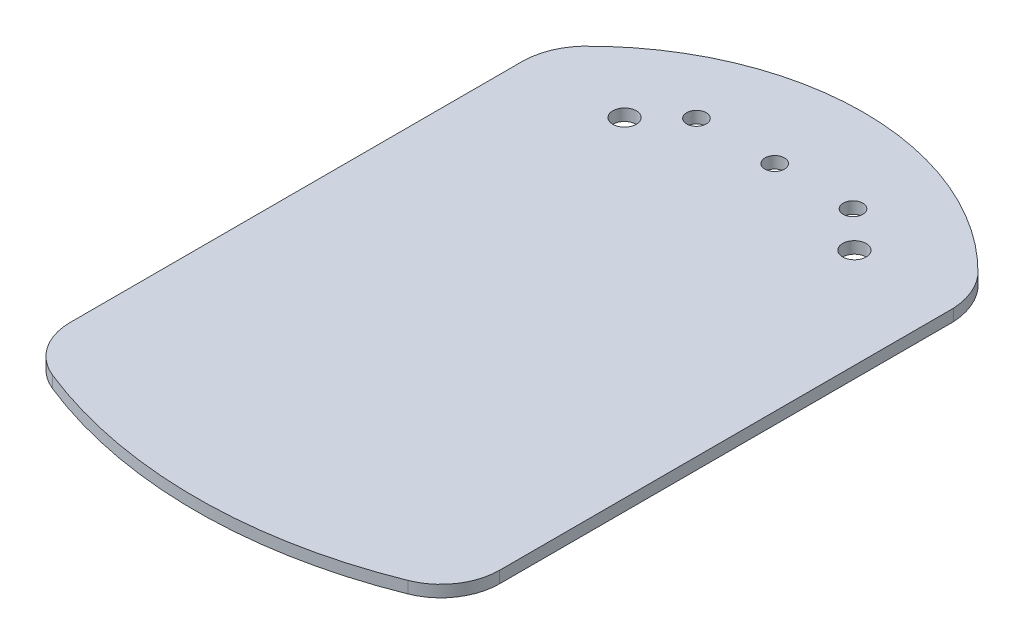
SolidWorks part; units mm, degrees
ref_plane "Front Plane" through (0, 0, 0) normal (0, 0, 1) x (1, 0, 0)
ref_plane "Top Plane" through (0, 0, 0) normal (0, 1, 0) x (1, 0, 0)
ref_plane "Right Plane" through (0, 0, 0) normal (1, 0, 0) x (0, 0, -1)
sketch "Sketch2" plane through (0, 0, 0) normal (0, 1, 0) x (1, 0, 0)
  line L0 (0, 42.2024) -> (20, 42.2024) construction
  line L2 (-54.8439, -82.9506) -> (-54.8439, 33.0807)
  line L4 (54.8439, -82.9506) -> (54.8439, 33.0807)
  line L5 (-38.4122, -53.1213) -> (35.0784, 48.5109) construction
  line L6 (-35.0784, 48.5109) -> (38.4122, -53.1213) construction
  line L7 (0, 42.2024) -> (-20, 42.2024) construction
  arc A0 (-50.5821, 43.5541) -> (50.5821, 43.5541) centre (0, -5.7807) cw
  arc A1 (-45.432, -96.8708) -> (45.432, -96.8708) centre (0, 16.303) ccw
  arc A3 (54.8439, -82.9506) -> (45.432, -96.8708) centre (39.8439, -82.9506) cw
  arc A4 (-45.432, -96.8708) -> (-54.8439, -82.9506) centre (-39.8439, -82.9506) cw
  circle A6 centre (29.3596, 33.197) radius 3
  circle A7 centre (-29.3596, 33.197) radius 3
  circle A8 centre (0, 42.2024) radius 2.5
  circle A9 centre (20, 42.2024) radius 2.5
  circle A10 centre (-20, 42.2024) radius 2.5
  arc A11 (50.5821, 43.5541) -> (54.8439, 33.0807) centre (37.3603, 32.0701) cw
  arc A12 (-54.8439, 33.0807) -> (-50.5821, 43.5541) centre (-38.2098, 32.4157) cw
  point P0 (0, 0)
  dimension "D2" = 2
  dimension "D3" = 20
  dimension "D5" = 20
  dimension "D4" = 2
extrude "Boss-Extrude1" add sketch "Sketch2" along normal blind 3
